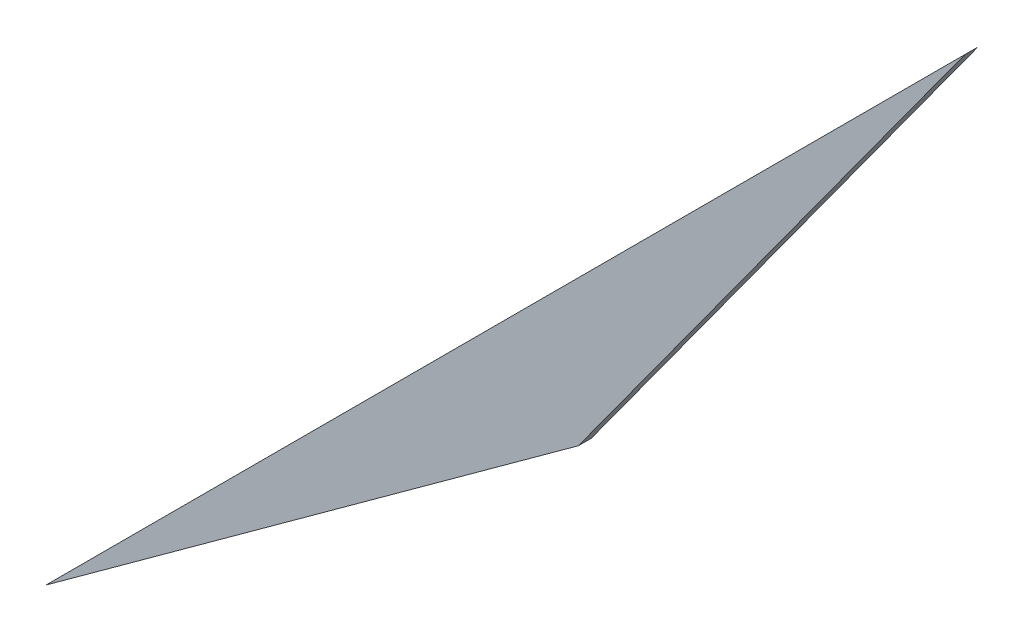
SolidWorks part; units mm, degrees
ref_plane "Front" through (0, 0, 0) normal (0, 0, 1) x (1, 0, 0)
ref_plane "Top" through (0, 0, 0) normal (0, 1, 0) x (1, 0, 0)
ref_plane "Right" through (0, 0, 0) normal (1, 0, 0) x (0, 0, -1)
sketch "Sketch1" plane through (0, 0, 0) normal (0, 0, 1) x (1, 0, 0)
  line L0 (-372.5761, 145.7797) -> (-241.2174, 241.2174)
  line L1 (-241.2174, 241.2174) -> (-145.7797, 372.5761)
  line L2 (-220.2814, 270.0333) -> (-169.3385, 340.1502) construction
  line L4 (-340.1502, 169.3385) -> (-270.0333, 220.2814) construction
  line L5 (-145.7797, 372.5761) -> (-372.5761, 145.7797)
  line L6 (-259.1779, 259.1779) -> (-241.2174, 241.2174) construction
  dimension "D1" = 25.4
extrude "Extrude1" add sketch "Sketch1" along normal blind 3.175
sketch "Sketch2" plane through (0, 0, 3.175) normal (0, 0, 1) x (1, 0, 0)
  circle A0 centre (0, -361.95) radius 3.9688
  circle A1 centre (0, -361.95) radius 3.556 construction
  dimension "D1" = 7.9375
extrude "Cut-Extrude1" cut sketch "Sketch2" against normal up to next
